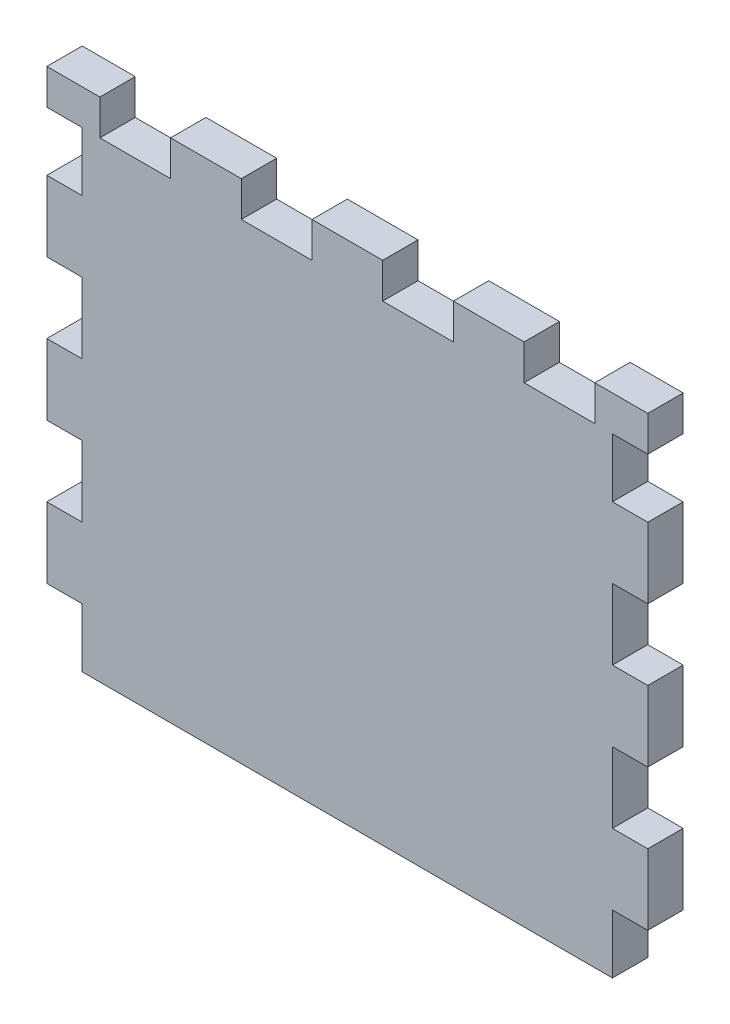
SolidWorks part; units mm, degrees
ref_plane "Front Plane" through (0, 0, 0) normal (0, 0, 1) x (1, 0, 0)
ref_plane "Top Plane" through (0, 0, 0) normal (0, 1, 0) x (1, 0, 0)
ref_plane "Right Plane" through (0, 0, 0) normal (1, 0, 0) x (0, 0, -1)
sketch "Sketch1" plane through (0, 0, 0) normal (0, 0, 1) x (1, 0, 0)
  line L1 (-22.5, 20) -> (22.5, 20)
  line L2 (-22.5, 20) -> (-22.5, -20)
  line L3 (-22.5, -20) -> (22.5, -20)
  line L4 (22.5, 20) -> (22.5, -20)
  line L5 (-22.5, 20) -> (22.5, -20) construction
  line L6 (-22.5, -20) -> (22.5, 20) construction
  point P0 (0, 0)
  dimension "D1" = 40
  dimension "D2" = 45
extrude "Boss-Extrude1" add sketch "Sketch1" along normal blind 3
sketch "Sketch2" plane through (-22.5, 0, 0) normal (-1, 0, 0) x (0, 0, 1)
  line L0 (0, 0) -> (3, 0) construction
  line L1 (0, 20) -> (0, -20) construction
  line L2 (3, 20) -> (3, -20) construction
  line L4 (3, 3) -> (0, 3)
  line L5 (3, 3) -> (3, -3)
  line L6 (3, -3) -> (0, -3)
  line L7 (0, 3) -> (0, -3)
  line L8 (3, 3) -> (0, -3) construction
  line L9 (3, -3) -> (0, 3) construction
  point P6 (1.5, 0)
  dimension "D1" = 6
extrude "Boss-Extrude2" add sketch "Sketch2" along normal blind 3
pattern_linear "LPattern1" count 2 spacing 12 along (0, -1, 0) count 2 spacing 12 along (0, 1, 0) of "Boss-Extrude2"
sketch "Sketch3" plane through (0, 20, 0) normal (0, 1, 0) x (1, 0, 0)
  line L0 (0, 0) -> (0, -3) construction
  line L1 (22.5, 0) -> (-22.5, 0) construction
  line L2 (22.5, -3) -> (-22.5, -3) construction
  line L4 (-3, 0) -> (3, 0)
  line L5 (-3, 0) -> (-3, -3)
  line L6 (-3, -3) -> (3, -3)
  line L7 (3, 0) -> (3, -3)
  line L8 (-3, 0) -> (3, -3) construction
  line L9 (-3, -3) -> (3, 0) construction
  point P6 (0, -1.5)
  dimension "D1" = 6
extrude "Boss-Extrude3" add sketch "Sketch3" along normal blind 3
pattern_linear "LPattern2" count 3 spacing 12 along (-1, 0, 0) count 3 spacing 12 along (1, 0, 0) of "Boss-Extrude3"
ref_plane "Plane1" through (0, 0, 0) normal (1, 0, 0) x (0, 0, -1)
sketch "Sketch5" [suppressed] plane through (0, 0, 0) normal (0, 0, -1) x (-1, 0, 0)
  line L0 (21, 23) -> (27, 23) construction
  line L1 (27, 20) -> (22.5, 20)
  line L2 (27, 20) -> (27, 23)
  line L3 (27, 23) -> (22.5, 23)
  line L4 (22.5, 20) -> (22.5, 23)
  line L5 (27, 20) -> (22.5, 23) construction
  line L6 (27, 23) -> (22.5, 20) construction
  line L8 (22.5, 20) -> (22.5, 15) construction
  point P4 (24.75, 21.5)
sketch "Sketch6" plane through (0, 23, 0) normal (0, 1, 0) x (1, 0, 0)
  line L0 (27, 0) -> (21, 0) construction
  line L1 (27, -3) -> (25.5, -3)
  line L2 (27, -3) -> (27, 0)
  line L3 (27, 0) -> (25.5, 0)
  line L4 (25.5, -3) -> (25.5, 0)
  line L5 (27, -3) -> (25.5, 0) construction
  line L6 (27, 0) -> (25.5, -3) construction
  line L8 (21, 0) -> (21, -3) construction
  point P4 (26.25, -1.5)
  dimension "D1" = 4.5
extrude "Cut-Extrude2" cut sketch "Sketch6" against normal up to next (3 mm away)
mirror "Mirror1" about plane through (0, 0, 0) normal (1, 0, 0) of "LPattern1", "Boss-Extrude2"
mirror "Mirror2" about plane through (0, 0, 0) normal (1, 0, 0) of "Cut-Extrude2"
